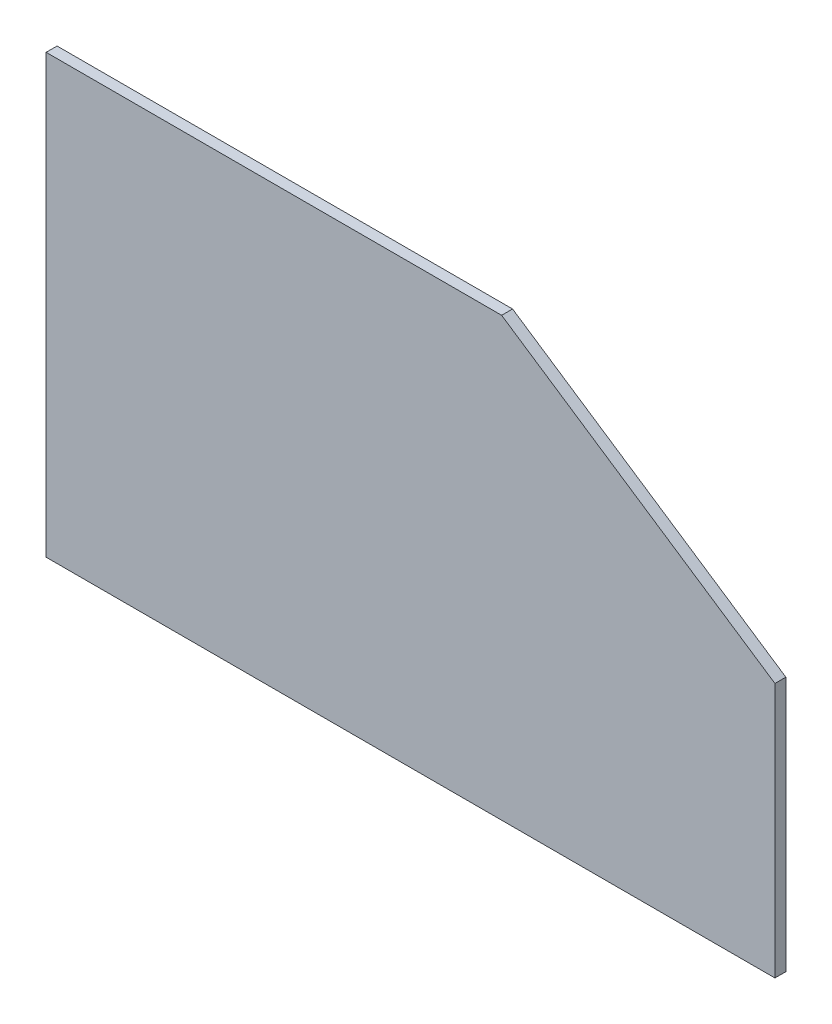
SolidWorks part; units mm, degrees
ref_plane "Front Plane" through (0, 0, 0) normal (0, 0, 1) x (1, 0, 0)
ref_plane "Top Plane" through (0, 0, 0) normal (0, 1, 0) x (1, 0, 0)
ref_plane "Right Plane" through (0, 0, 0) normal (1, 0, 0) x (0, 0, -1)
sketch "Sketch1" plane through (0, 0, 0) normal (0, 0, 1) x (1, 0, 0)
  line L0 (0, 0) -> (0, 120)
  line L1 (0, 120) -> (125, 120)
  line L2 (125, 120) -> (200, 70)
  line L3 (200, 70) -> (200, 0)
  line L4 (200, 0) -> (0, 0)
  dimension "D1" = 200
  dimension "D2" = 120
  dimension "D3" = 125
  dimension "D4" = 70
extrude "Boss-Extrude1" add sketch "Sketch1" along normal blind 3
